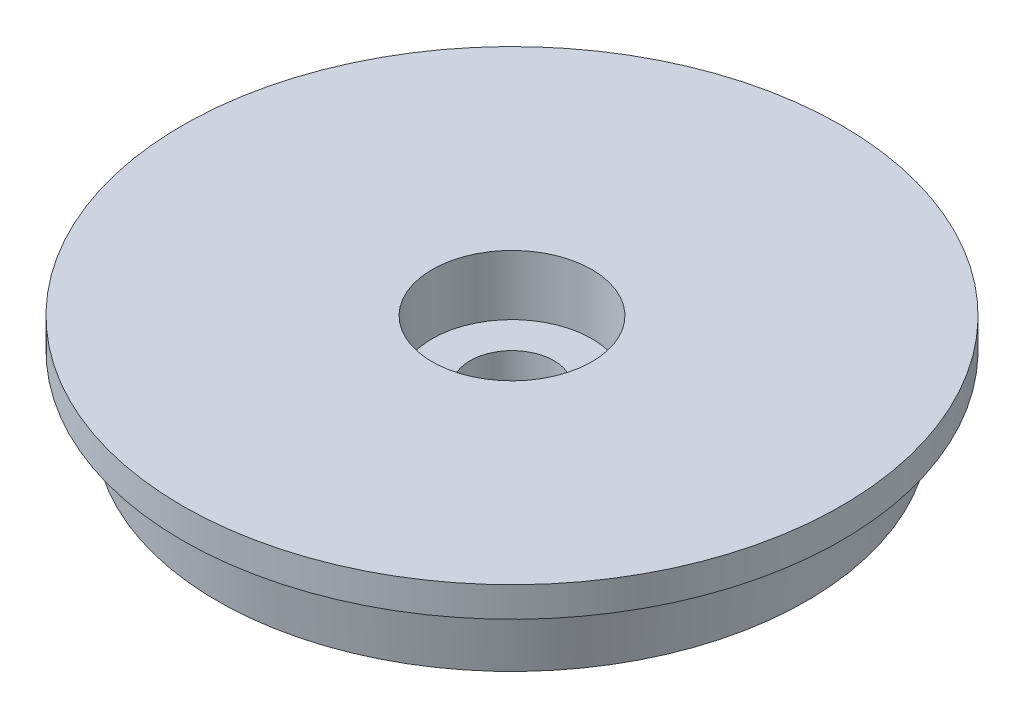
SolidWorks part; units mm, degrees
ref_plane "Front Plane" through (0, 0, 0) normal (0, 0, 1) x (1, 0, 0)
ref_plane "Top Plane" through (0, 0, 0) normal (0, 1, 0) x (1, 0, 0)
ref_plane "Right Plane" through (0, 0, 0) normal (1, 0, 0) x (0, 0, -1)
sketch "Sketch1" plane through (0, 0, 0) normal (0, 0, 1) x (1, 0, 0)
  circle A0 centre (0, 0) radius 30.6393
extrude "Boss-Extrude1" [suppressed] add sketch "Sketch1" along normal blind 1
sketch "Sketch2" [suppressed] plane through (0, 0, 1) normal (0, 0, 1) x (1, 0, 0)
  circle A0 centre (0, 0) radius 15
  dimension "D1" = 30
extrude "Boss-Extrude2" [suppressed] add sketch "Sketch2" along normal blind 3
sketch "Sketch3" [suppressed] plane through (0, 0, 0) normal (0, 0, -1) x (-1, 0, 0)
  circle A0 centre (0, 0) radius 4
  dimension "D1" = 8
extrude "Cut-Extrude1" [suppressed] cut sketch "Sketch3" against normal blind 3
sketch "Sketch4" [suppressed] plane through (0, 0, 3) normal (0, 0, -1) x (-1, 0, 0)
  circle A0 centre (0, 0) radius 2.1
  dimension "D1" = 4.2
extrude "Cut-Extrude2" [suppressed] cut sketch "Sketch4" against normal blind 3
sketch "Sketch5" plane through (0, 0, 0) normal (1, 0, 0) x (0, 0, -1)
  line L0 (0, 0) -> (0, 4.6706) construction
  line L1 (2.1, 0) -> (2.1, 2)
  line L2 (2.1, 2) -> (4, 2)
  line L3 (4, 2) -> (4, 5)
  line L4 (4, 5) -> (16.5, 5)
  line L5 (16.5, 5) -> (16.5, 3.5)
  line L6 (16.5, 3.5) -> (15.1, 3.5)
  line L7 (15.1, 3.5) -> (14.75, 0)
  line L8 (14.75, 0) -> (2.1, 0)
  point P10 (17.7231, -0.4912)
  point P12 (0, 0)
  point P13 (14.3939, -0.218)
  dimension "D1" = 4.2
  dimension "D2" = 8
  dimension "D3" = 3
  dimension "D4" = 2
  dimension "D5" = 1.5
  dimension "D6" = 30.2
  dimension "D7" = 29.5
  dimension "D8" = 33
revolve "Revolve1" add sketch "Sketch5" angle 360 about L0
